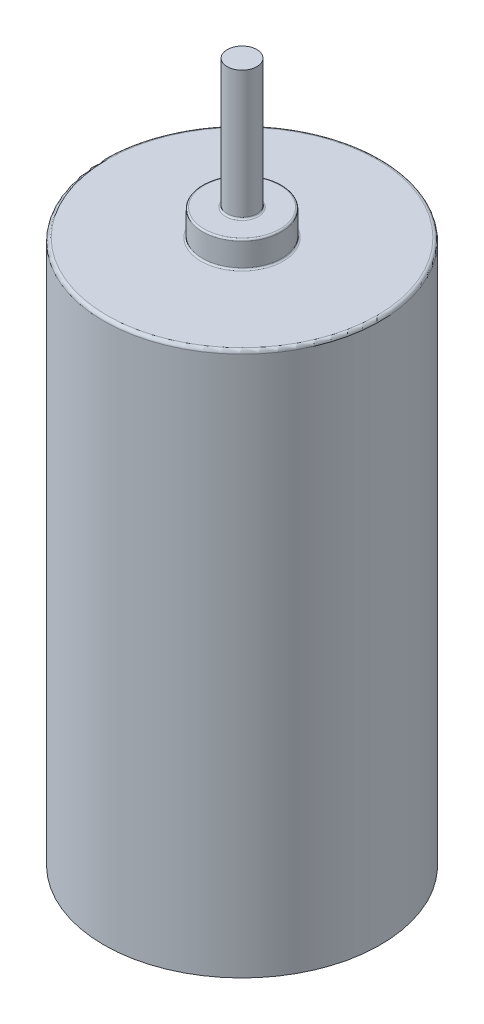
SolidWorks part; units mm, degrees
ref_plane "Front Plane" through (0, 0, 0) normal (0, 0, 1) x (1, 0, 0)
ref_plane "Top Plane" through (0, 0, 0) normal (0, 1, 0) x (1, 0, 0)
ref_plane "Right Plane" through (0, 0, 0) normal (1, 0, 0) x (0, 0, -1)
sketch "Sketch1" plane through (0, 0, 0) normal (0, 1, 0) x (1, 0, 0)
  circle A0 centre (0, 0) radius 4.2
extrude "Boss-Extrude1" add sketch "Sketch1" along normal blind 16.51
ref_plane "Plane1" through (0, 16.51, 0) normal (0, 1, 0) x (1, 0, 0)
sketch "Sketch2" plane through (0, 16.51, 0) normal (0, 1, 0) x (1, 0, 0)
  circle A0 centre (0, 0) radius 1.2
extrude "Boss-Extrude2" add sketch "Sketch2" along normal blind 0.8
ref_plane "Plane2" through (0, 17.31, 0) normal (0, 1, 0) x (1, 0, 0)
sketch "Sketch3" plane through (0, 17.31, 0) normal (0, 1, 0) x (1, 0, 0)
  circle A0 centre (0, 0) radius 0.45
extrude "Boss-Extrude3" add sketch "Sketch3" along normal blind 3.92
fillet "Fillet3" radius 0.05 3 edges at (0, 16.51, 1.2) (0, 17.31, 0.45) (0, 17.31, 1.2)
fillet "Fillet4" radius 0.1 1 edges at (0, 16.51, 4.2)
